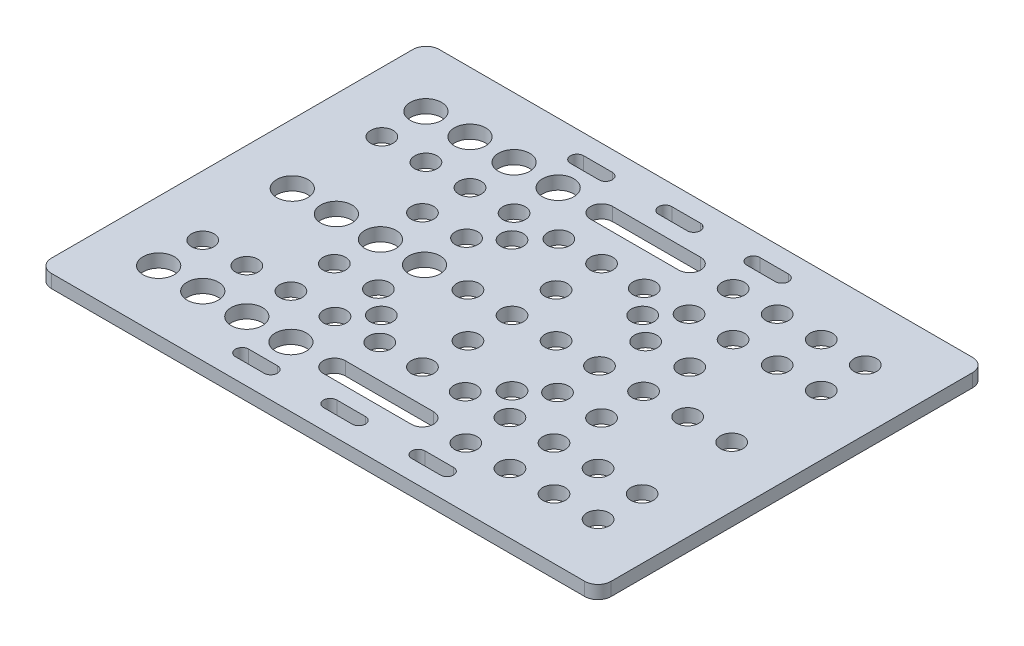
SolidWorks part; units mm, degrees
material "6061-T6 (SS)"
ref_plane "Front Plane" through (0, 0, 0) normal (0, 0, 1) x (1, 0, 0)
ref_plane "Top Plane" through (0, 0, 0) normal (0, 1, 0) x (1, 0, 0)
ref_plane "Right Plane" through (0, 0, 0) normal (1, 0, 0) x (0, 0, -1)
sketch "Sketch1" plane through (0, 0, 0) normal (0, 1, 0) x (1, 0, 0)
  line L0 (0, 0) -> (63.5, 0) construction
  line L1 (60.5, -44) -> (-60.5, -44)
  line L2 (63.5, -41) -> (63.5, 41)
  line L3 (60.5, 44) -> (-60.5, 44)
  line L4 (-63.5, -41) -> (-63.5, 41)
  line L5 (0, 44) -> (0, 0) construction
  line L6 (-49.85, 30.32) -> (-39.85, 30.32) construction
  line L7 (49.85, 30.32) -> (39.85, 30.32) construction
  line L8 (49.85, 0) -> (39.85, 0) construction
  line L9 (10, 30.32) -> (-10, 30.32) construction
  line L10 (10, 27.82) -> (-10, 27.82)
  line L11 (10, 32.82) -> (-10, 32.82)
  line L12 (3.25, 38) -> (-3.25, 38) construction
  line L13 (3.25, 36.5) -> (-3.25, 36.5)
  line L14 (3.25, 39.5) -> (-3.25, 39.5)
  line L15 (-16.75, 38) -> (-23.25, 38) construction
  line L16 (-16.75, 36.5) -> (-23.25, 36.5)
  line L17 (-16.75, 39.5) -> (-23.25, 39.5)
  line L18 (16.75, 38) -> (23.25, 38) construction
  line L19 (16.75, 36.5) -> (23.25, 36.5)
  line L20 (16.75, 39.5) -> (23.25, 39.5)
  line L21 (10, -30.32) -> (-10, -30.32) construction
  line L22 (10, -27.82) -> (-10, -27.82)
  line L23 (10, -32.82) -> (-10, -32.82)
  line L24 (-16.75, -38) -> (-23.25, -38) construction
  line L25 (-16.75, -36.5) -> (-23.25, -36.5)
  line L26 (-16.75, -39.5) -> (-23.25, -39.5)
  line L27 (3.25, -38) -> (-3.25, -38) construction
  line L28 (3.25, -36.5) -> (-3.25, -36.5)
  line L29 (3.25, -39.5) -> (-3.25, -39.5)
  line L30 (16.75, -38) -> (23.25, -38) construction
  line L31 (16.75, -36.5) -> (23.25, -36.5)
  line L32 (16.75, -39.5) -> (23.25, -39.5)
  arc A0 (-60.5, -44) -> (-63.5, -41) centre (-60.5, -41) cw
  arc A1 (60.5, -44) -> (63.5, -41) centre (60.5, -41) ccw
  arc A2 (63.5, 41) -> (60.5, 44) centre (60.5, 41) ccw
  arc A3 (-60.5, 44) -> (-63.5, 41) centre (-60.5, 41) ccw
  circle A4 centre (-39.85, 30.32) radius 3.55
  circle A5 centre (0, 10) radius 2.55
  circle A6 centre (0, 0) radius 2.55
  circle A7 centre (10, 0) radius 2.55
  circle A8 centre (-10, 0) radius 2.55
  circle A9 centre (-49.85, 30.32) radius 3.55
  circle A10 centre (-49.85, 0) radius 3.55
  circle A11 centre (-49.85, -30.32) radius 3.55
  circle A12 centre (-20.32, 10) radius 2.55
  circle A13 centre (-30.32, 10) radius 2.55
  circle A14 centre (-14.825, 14.825) radius 2.55
  circle A15 centre (0, 20.32) radius 2.55
  circle A16 centre (-49.85, 20.32) radius 2.55
  circle A17 centre (-39.85, 20.32) radius 2.55
  circle A18 centre (-29.85, 20.32) radius 2.55
  circle A19 centre (-39.85, 0) radius 3.55
  circle A20 centre (14.825, 14.825) radius 2.55
  circle A21 centre (20.32, 10) radius 2.55
  circle A22 centre (30.32, 10) radius 2.55
  circle A23 centre (39.85, 30.32) radius 2.55
  circle A24 centre (49.85, 30.32) radius 2.55
  circle A25 centre (49.85, 0) radius 2.55
  circle A26 centre (30.32, -10) radius 2.55
  circle A27 centre (49.85, -30.32) radius 2.55
  circle A28 centre (29.85, 30.32) radius 2.55
  circle A29 centre (20.32, -10) radius 2.55
  circle A30 centre (0, -10) radius 2.55
  circle A31 centre (14.825, -14.825) radius 2.55
  circle A32 centre (-29.85, 0) radius 3.55
  circle A33 centre (-19.85, 20.32) radius 2.55
  circle A34 centre (-9.69, 20.32) radius 2.55
  circle A35 centre (9.69, 20.32) radius 2.55
  circle A36 centre (-19.85, 0) radius 3.55
  circle A37 centre (-14.825, -14.825) radius 2.55
  circle A38 centre (-20.32, -10) radius 2.55
  circle A39 centre (-30.32, -10) radius 2.55
  circle A40 centre (-29.85, 30.32) radius 3.55
  circle A41 centre (-19.85, 30.32) radius 3.55
  circle A42 centre (19.85, 30.32) radius 2.55
  circle A43 centre (19.85, 20.32) radius 2.55
  circle A44 centre (29.85, 20.32) radius 2.55
  circle A45 centre (39.85, 20.32) radius 2.55
  circle A46 centre (49.85, 20.32) radius 2.55
  circle A47 centre (39.85, 0) radius 2.55
  circle A48 centre (29.85, 0) radius 2.55
  circle A49 centre (19.85, 0) radius 2.55
  circle A50 centre (19.85, -30.32) radius 2.55
  circle A51 centre (29.85, -30.32) radius 2.55
  circle A52 centre (0, -20.32) radius 2.55
  circle A53 centre (39.85, -30.32) radius 2.55
  circle A54 centre (49.85, -20.32) radius 2.55
  circle A55 centre (39.85, -20.32) radius 2.55
  circle A56 centre (29.85, -20.32) radius 2.55
  circle A57 centre (19.85, -20.32) radius 2.55
  circle A58 centre (9.69, -20.32) radius 2.55
  circle A59 centre (-9.69, -20.32) radius 2.55
  circle A60 centre (-19.85, -20.32) radius 2.55
  circle A61 centre (-29.85, -20.32) radius 2.55
  circle A62 centre (-39.85, -20.32) radius 2.55
  circle A63 centre (-49.85, -20.32) radius 2.55
  circle A64 centre (-19.85, -30.32) radius 3.55
  circle A65 centre (-29.85, -30.32) radius 3.55
  circle A66 centre (-39.85, -30.32) radius 3.55
  arc A67 (10, 27.82) -> (10, 32.82) centre (10, 30.32) ccw
  arc A68 (-10, 32.82) -> (-10, 27.82) centre (-10, 30.32) ccw
  arc A69 (3.25, 36.5) -> (3.25, 39.5) centre (3.25, 38) ccw
  arc A70 (-3.25, 39.5) -> (-3.25, 36.5) centre (-3.25, 38) ccw
  arc A71 (-16.75, 36.5) -> (-16.75, 39.5) centre (-16.75, 38) ccw
  arc A72 (-23.25, 39.5) -> (-23.25, 36.5) centre (-23.25, 38) ccw
  arc A73 (16.75, 36.5) -> (16.75, 39.5) centre (16.75, 38) cw
  arc A74 (23.25, 39.5) -> (23.25, 36.5) centre (23.25, 38) cw
  arc A75 (10, -27.82) -> (10, -32.82) centre (10, -30.32) cw
  arc A76 (-10, -32.82) -> (-10, -27.82) centre (-10, -30.32) cw
  arc A77 (-16.75, -36.5) -> (-16.75, -39.5) centre (-16.75, -38) cw
  arc A78 (-23.25, -39.5) -> (-23.25, -36.5) centre (-23.25, -38) cw
  arc A79 (3.25, -36.5) -> (3.25, -39.5) centre (3.25, -38) cw
  arc A80 (-3.25, -39.5) -> (-3.25, -36.5) centre (-3.25, -38) cw
  arc A81 (16.75, -36.5) -> (16.75, -39.5) centre (16.75, -38) ccw
  arc A82 (23.25, -39.5) -> (23.25, -36.5) centre (23.25, -38) ccw
  point P0 (0, 0)
  point P149 (0, 30.32)
  point P156 (0, 38)
  point P162 (-20, 38)
  point P170 (20, 38)
  point P177 (0, -30.32)
  point P184 (-20, -38)
  point P191 (0, -38)
  point P198 (20, -38)
  dimension "D2" = 3
  dimension "D3" = 5.1
  dimension "D5" = 7.1
  dimension "D7" = 4
  dimension "D10" = 10
  dimension "D19" = 10
  dimension "D1" = 88
  dimension "D4" = 10
  dimension "D6" = 60.64
  dimension "D8" = 13.65
  dimension "D9" = 127
  dimension "D11" = 10
  dimension "D12" = 4
  dimension "D13" = 10
  dimension "D14" = 10
  dimension "D15" = 20.32
  dimension "D16" = 99.7
  dimension "D17" = 4
  dimension "D18" = 10
  dimension "D20" = 29.65
  dimension "D21" = 29.65
  dimension "D22" = 10.16
  dimension "D24" = 10
  dimension "D25" = 5
  dimension "D26" = 20
  dimension "D27" = 6.5
  dimension "D28" = 3
  dimension "D29" = 20
  dimension "D30" = 60.64
  dimension "D31" = 76
  dimension "D23" = 4
extrude "Boss-Extrude1" add sketch "Sketch1" along normal blind 3
